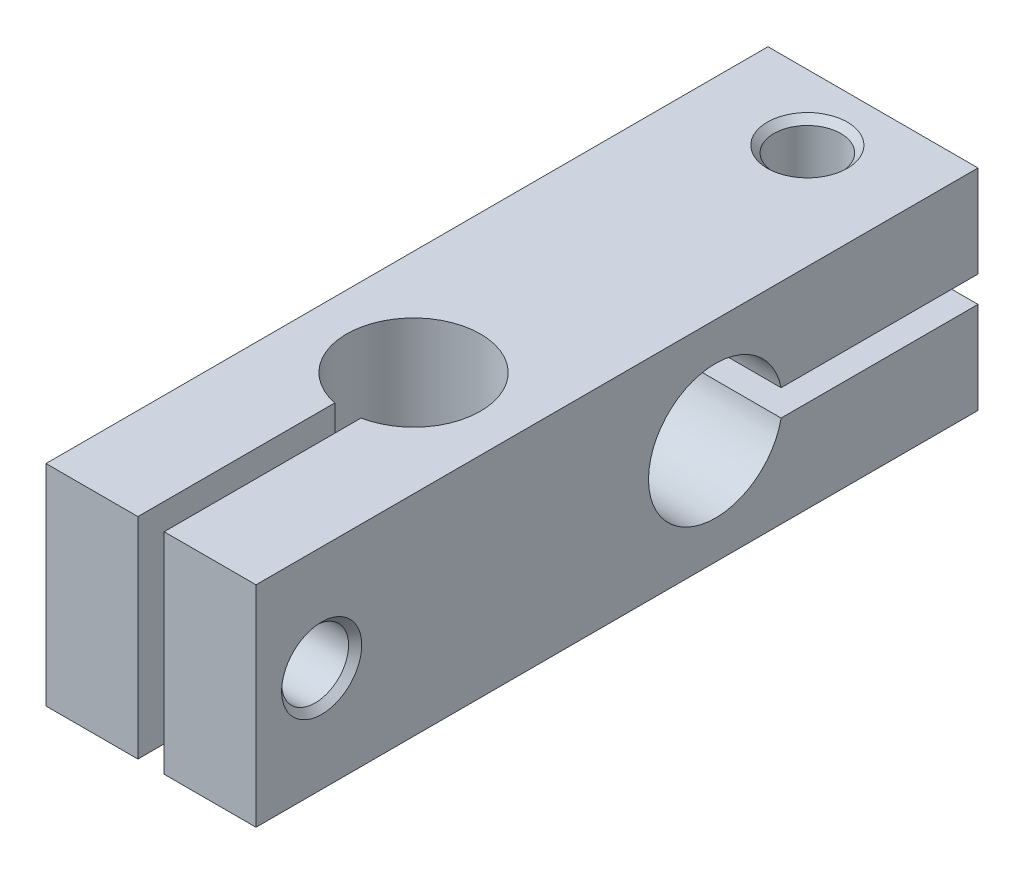
SolidWorks part; units mm, degrees
material "6063-T6"
ref_plane "Front Plane" through (0, 0, 0) normal (0, 0, 1) x (1, 0, 0)
ref_plane "Top Plane" through (0, 0, 0) normal (0, 1, 0) x (1, 0, 0)
ref_plane "Right Plane" through (0, 0, 0) normal (1, 0, 0) x (0, 0, -1)
sketch "Sketch1" plane through (0, 0, 0) normal (0, 0, 1) x (1, 0, 0)
  line L1 (8, -8) -> (-8, -8)
  line L2 (8, -8) -> (8, 8)
  line L3 (8, 8) -> (-8, 8)
  line L4 (-8, -8) -> (-8, 8)
  line L5 (8, -8) -> (-8, 8) construction
  line L6 (8, 8) -> (-8, -8) construction
  point P0 (0, 0)
  dimension "D1" = 16
  dimension "D2" = 16
extrude "Base" add sketch "Sketch1" along normal blind 55
sketch "Sketch2" plane through (0, 8, 0) normal (0, 1, 0) x (1, 0, 0)
  line L0 (-1, -55) -> (-1, -39)
  line L1 (8, -55) -> (-8, -55) construction
  line L2 (1, -55) -> (1, -39)
  line L3 (0, 0) -> (0, -9.2456) construction
  line L4 (-1, -39) -> (1, -39)
  dimension "D1" = 16
  dimension "D3" = 2
extrude "RodSlot" cut sketch "Sketch2" against normal through all
hole_wizard "Ø5.1 (5.1) free hole for screw" positions "Sketch7" profile "Sketch8" hole size "Ø5.1" standard "ANSI Metric"
sketch "Sketch7" plane through (8, 0, 0) normal (1, 0, 0) x (0, 0, -1)
  line L0 (-55, -8) -> (-55, 8) construction
  point P0 (-50, 0)
  dimension "D1" = 5
sketch "Sketch8" plane through (8, 0, 50) normal (0, 1, 0) x (0, 0, -1)
  line L0 (0, 0) -> (0, 8.5562)
  line L1 (0, 8.5562) -> (2.55, 7.5)
  line L2 (2.55, 7.5) -> (2.55, 0.5)
  line L3 (2.55, 0.5) -> (3.05, 0)
  line L5 (3.05, 0) -> (0, 0)
  line L6 (-2.55, 0.5) -> (-3.05, 0) construction
  line L10 (0, 8.5562) -> (-2.55, 7.5) construction
  line L11 (0, -6.35) -> (0, 107.95) construction
  dimension "Hole Dia." = 5.1
  dimension "Hole Depth" = 7.5
  dimension "Near C'Sink Dia." = 6.1
  dimension "Near C'Sink Angle" = 90
  dimension "Drill Angle" = 135
hole_wizard "M5x0.8 Tapped Hole for rod screw" positions "Sketch4" profile "Sketch5" tap size "M5x0.8" standard "ANSI Metric"
sketch "Sketch4" plane through (-8, 0, 0) normal (-1, 0, 0) x (0, 0, 1)
  point P0 (50, 0)
cosmetic thread "Hole Thread1" parameters "D1"=7, "D2"=5
sketch "Sketch5" plane through (-8, 0, 50) normal (0, 1, 0) x (0, 0, 1)
  line L0 (0, 0) -> (0, 8.9)
  line L1 (0, 8.9) -> (2.1, 7.6382)
  line L2 (2.1, 7.6382) -> (2.1, 0)
  line L5 (2.1, 0) -> (0, 0)
  line L10 (0, 8.9) -> (-2.1, 7.6382) construction
  line L11 (0, -6.35) -> (0, 107.95) construction
  dimension "Tap Drill Dia." = 4.2
  dimension "Tap Drill Depth" = 8.9
  dimension "Drill Angle" = 118
hole_wizard "Ø10.2 (10.2) Rod Hole" positions "Sketch11" profile "Sketch12" hole size "Ø10.2" standard "ANSI Metric" end condition through all
sketch "Sketch11" plane through (0, 8, 0) normal (0, 1, 0) x (1, 0, 0)
  line L1 (8, -55) -> (1, -55) construction
  point P0 (0, -35)
  dimension "D1" = 20
sketch "Sketch12" plane through (0, 8, 35) normal (1, 0, 0) x (0, 0, 1)
  line L0 (0, 0) -> (0, 16)
  line L1 (0, 16) -> (5.1, 16)
  line L2 (5.1, 16) -> (5.1, 0)
  line L5 (5.1, 0) -> (0, 0)
  line L11 (0, -6.35) -> (0, 107.95) construction
  dimension "Thru Hole Dia." = 10.2
  dimension "Thru Hole Depth" = 16
sketch "Sketch13" plane through (-8, 0, 0) normal (-1, 0, 0) x (0, 0, 1)
  line L0 (0, 8) -> (0, -8) construction
  line L1 (0, 1) -> (20, 1)
  line L2 (0, 1) -> (0, -1)
  line L3 (0, -1) -> (20, -1)
  line L4 (20, 1) -> (20, -1)
  point P6 (0, 0)
  dimension "D1" = 2
  dimension "D2" = 20
extrude "Rod2Slot" cut sketch "Sketch13" against normal through all
hole_wizard "Ø10.2 (10.2) Rod2 Hole" positions "Sketch14" profile "Sketch15" hole size "Ø10.2" standard "ANSI Metric" end condition through all
sketch "Sketch14" plane through (-8, 0, 0) normal (-1, 0, 0) x (0, 1, 0)
  point P0 (0, -20)
  dimension "D1" = 20
sketch "Sketch15" plane through (-8, 0, 20) normal (0, 1, 0) x (0, 0, 1)
  line L0 (0, 0) -> (0, 16)
  line L1 (0, 16) -> (5.1, 16)
  line L2 (5.1, 16) -> (5.1, 0)
  line L5 (5.1, 0) -> (0, 0)
  line L11 (0, -6.35) -> (0, 107.95) construction
  dimension "Thru Hole Dia." = 10.2
  dimension "Thru Hole Depth" = 16
hole_wizard "Ø5.1 (5.1) Diameter Hole1" positions "Sketch16" profile "Sketch17" hole size "Ø5.1" standard "ANSI Metric"
sketch "Sketch16" plane through (0, 8, 0) normal (0, 1, 0) x (0, 0, -1)
  line L1 (0, -8) -> (0, 8) construction
  point P0 (-5, 0)
  dimension "D1" = 5
sketch "Sketch17" plane through (0, 8, 5) normal (1, 0, 0) x (0, 0, 1)
  line L0 (0, 0) -> (0, 8.5562)
  line L1 (0, 8.5562) -> (2.55, 7.5)
  line L2 (2.55, 7.5) -> (2.55, 0.5)
  line L3 (2.55, 0.5) -> (3.05, 0)
  line L5 (3.05, 0) -> (0, 0)
  line L6 (-2.55, 0.5) -> (-3.05, 0) construction
  line L10 (0, 8.5562) -> (-2.55, 7.5) construction
  line L11 (0, -6.35) -> (0, 107.95) construction
  dimension "Hole Dia." = 5.1
  dimension "Hole Depth" = 7.5
  dimension "Near C'Sink Dia." = 6.1
  dimension "Near C'Sink Angle" = 90
  dimension "Drill Angle" = 135
hole_wizard "M5x0.8 Tapped Hole1" positions "Sketch19" profile "Sketch20" tap size "M5x0.8" standard "ANSI Metric"
sketch "Sketch19" plane through (0, -8, 0) normal (0, -1, 0) x (-1, 0, 0)
  line L0 (8, 0) -> (-8, 0) construction
  point P0 (0, -5)
  dimension "D1" = 5
sketch "Sketch20" plane through (0, -8, 5) normal (1, 0, 0) x (0, 0, -1)
  line L0 (0, 0) -> (0, 8.9)
  line L1 (0, 8.9) -> (2.1, 7.6382)
  line L2 (2.1, 7.6382) -> (2.1, 0)
  line L5 (2.1, 0) -> (0, 0)
  line L10 (0, 8.9) -> (-2.1, 7.6382) construction
  line L11 (0, -6.35) -> (0, 107.95) construction
  dimension "Tap Drill Dia." = 4.2
  dimension "Tap Drill Depth" = 8.9
  dimension "Drill Angle" = 118
cosmetic thread "Hole Thread2" parameters "D1"=7, "D2"=5
equation "\"D2@Sketch1\"=\"D1@Sketch1\""
